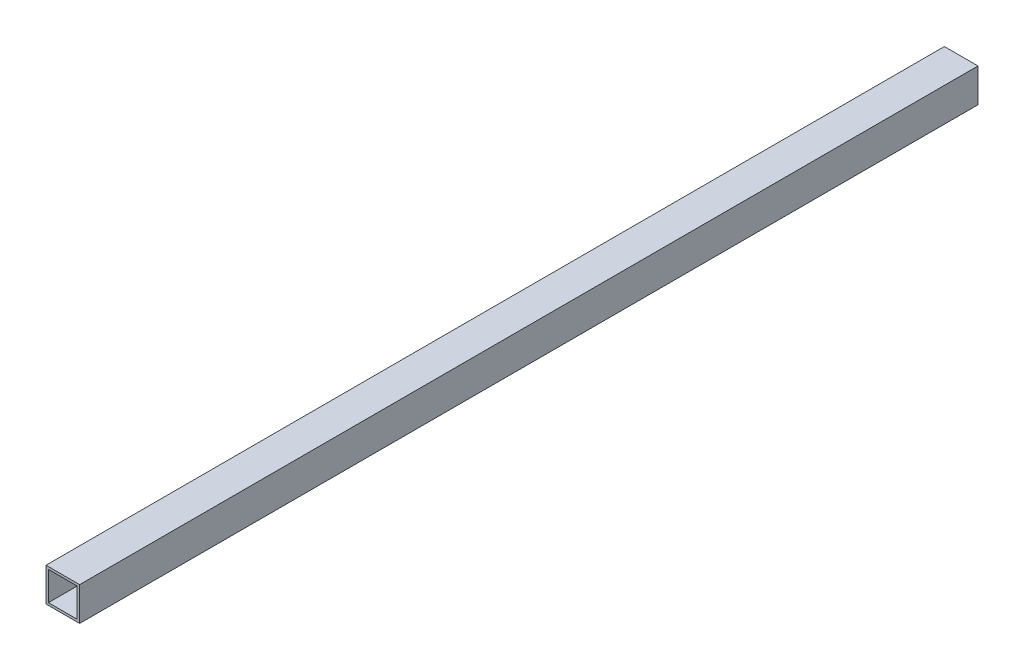
SolidWorks part; units mm, degrees
material "6061-T6 (SS)"
ref_plane "Front Plane" through (0, 0, 0) normal (0, 0, 1) x (1, 0, 0)
ref_plane "Top Plane" through (0, 0, 0) normal (0, 1, 0) x (1, 0, 0)
ref_plane "Right Plane" through (0, 0, 0) normal (1, 0, 0) x (0, 0, -1)
sketch "Sketch1" plane through (0, 0, 0) normal (0, 0, 1) x (1, 0, 0)
  line L0 (3.175, 41.275) -> (41.275, 41.275)
  line L1 (0, 0) -> (44.45, 0)
  line L2 (0, 0) -> (0, 44.45)
  line L3 (0, 44.45) -> (44.45, 44.45)
  line L4 (44.45, 0) -> (44.45, 44.45)
  line L5 (41.275, 3.175) -> (41.275, 41.275)
  line L6 (3.175, 3.175) -> (41.275, 3.175)
  line L7 (3.175, 3.175) -> (3.175, 41.275)
  dimension "D1" = 44.45
  dimension "D2" = 44.45
  dimension "D3" = 3.175
extrude "Boss-Extrude1" add sketch "Sketch1" along normal blind 1187.45
